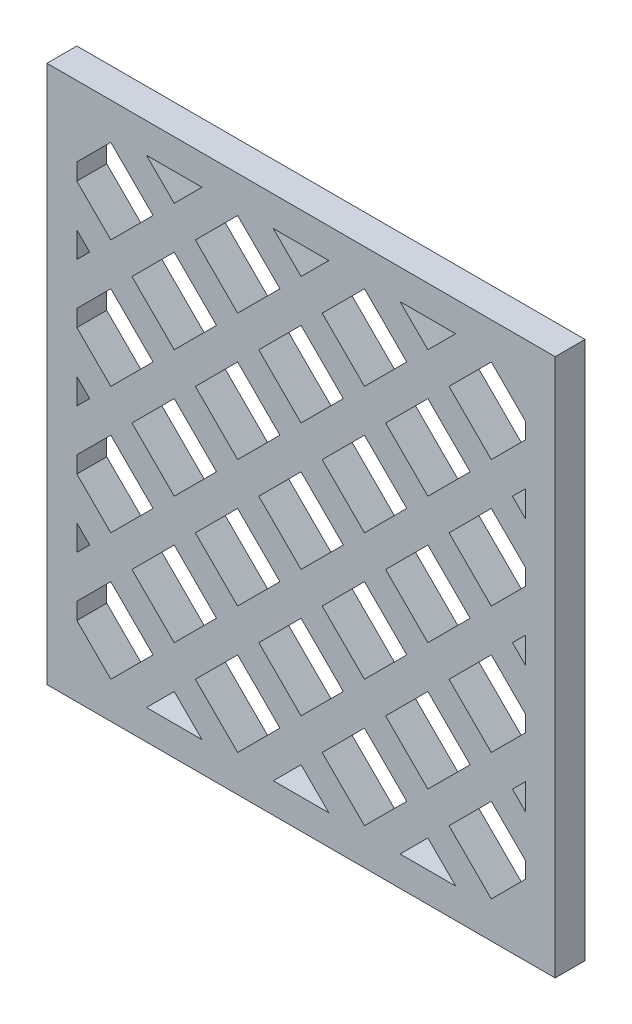
SolidWorks part; units mm, degrees
material "Balsa"
ref_plane "Alzado" through (0, 0, 0) normal (0, 0, 1) x (1, 0, 0)
ref_plane "Planta" through (0, 0, 0) normal (0, 1, 0) x (1, 0, 0)
ref_plane "Vista lateral" through (0, 0, 0) normal (1, 0, 0) x (0, 0, -1)
sketch "Croquis1" plane through (0, 0, 0) normal (0, 0, 1) x (1, 0, 0)
  line L0 (-75.1581, 75.2999) -> (-75.1581, -4.7001) construction
  line L1 (-80.1581, 80.2999) -> (4.8419, 80.2999)
  line L2 (-80.1581, 80.2999) -> (-80.1581, -9.7001)
  line L3 (-80.1581, -9.7001) -> (4.8419, -9.7001)
  line L4 (4.8419, 80.2999) -> (4.8419, -9.7001)
  line L5 (-75.1581, -4.7001) -> (-0.1581, -4.7001) construction
  line L6 (-0.1581, -4.7001) -> (-0.1581, 75.2999) construction
  line L7 (-0.1581, 75.2999) -> (-75.1581, 75.2999) construction
  line L8 (-37.6581, 80.2999) -> (-37.6581, -9.7001) construction
  line L9 (-80.1581, 35.2999) -> (4.8419, 35.2999) construction
  line L10 (-37.6581, 42.371) -> (-44.7291, 35.2999)
  line L11 (-44.7291, 35.2999) -> (-37.6581, 28.2288)
  line L12 (-37.6581, 28.2288) -> (-30.587, 35.2999)
  line L13 (-30.587, 35.2999) -> (-37.6581, 42.371)
  line L76 (-65.9423, 35.2999) -> (-58.8713, 28.2288)
  line L77 (-58.8713, 28.2288) -> (-51.8002, 35.2999)
  line L82 (-62.4068, 24.6933) -> (-69.4779, 31.7644)
  line L83 (-69.4779, 31.7644) -> (-75.1581, 26.0842)
  line L84 (-75.1581, 23.3024) -> (-69.4779, 17.6222)
  line L85 (-69.4779, 17.6222) -> (-62.4068, 24.6933)
  line L89 (-75.1581, 33.1552) -> (-72.8062, 35.5071)
  line L90 (-73.0134, 14.0867) -> (-75.1581, 16.2314)
  line L105 (-19.9804, 24.6933) -> (-27.0515, 31.7644)
  line L106 (-27.0515, 31.7644) -> (-34.1225, 24.6933)
  line L107 (-34.1225, 24.6933) -> (-27.0515, 17.6222)
  line L108 (-27.0515, 17.6222) -> (-19.9804, 24.6933)
  line L121 (-30.587, 14.0867) -> (-37.6581, 21.1578)
  line L122 (-37.6581, 21.1578) -> (-44.7291, 14.0867)
  line L123 (-44.7291, 14.0867) -> (-37.6581, 7.0156)
  line L124 (-37.6581, 7.0156) -> (-30.587, 14.0867)
  line L125 (-19.9804, 3.4801) -> (-27.0515, 10.5512)
  line L126 (-27.0515, 10.5512) -> (-34.1225, 3.4801)
  line L127 (-34.1225, 3.4801) -> (-27.0515, -3.591)
  line L128 (-27.0515, -3.591) -> (-19.9804, 3.4801)
  line L129 (-11.8002, -4.7001) -> (-16.4449, -0.0554)
  line L130 (-16.4449, -0.0554) -> (-21.0895, -4.7001)
  line L137 (-41.1936, 3.4801) -> (-48.2647, 10.5512)
  line L138 (-48.2647, 10.5512) -> (-55.3357, 3.4801)
  line L139 (-55.3357, 3.4801) -> (-48.2647, -3.591)
  line L140 (-48.2647, -3.591) -> (-41.1936, 3.4801)
  line L141 (-33.0134, -4.7001) -> (-37.6581, -0.0554)
  line L142 (-37.6581, -0.0554) -> (-42.3027, -4.7001)
  line L153 (-54.2266, -4.7001) -> (-58.8713, -0.0554)
  line L154 (-58.8713, -0.0554) -> (-63.5159, -4.7001)
  line L169 (-41.1936, 24.6933) -> (-48.2647, 31.7644)
  line L170 (-48.2647, 31.7644) -> (-55.3357, 24.6933)
  line L171 (-55.3357, 24.6933) -> (-48.2647, 17.6222)
  line L172 (-48.2647, 17.6222) -> (-41.1936, 24.6933)
  line L181 (-19.9804, -38.9463) -> (-27.0515, -31.8752) [skipped]
  line L182 (-27.0515, -31.8752) -> (-34.1225, -38.9463) [skipped]
  line L183 (-34.1225, -38.9463) -> (-27.0515, -46.0174) [skipped]
  line L184 (-27.0515, -46.0174) -> (-19.9804, -38.9463) [skipped]
  line L185 (-9.3738, -28.3397) -> (-16.4449, -21.2686) [skipped]
  line L186 (-16.4449, -21.2686) -> (-23.5159, -28.3397) [skipped]
  line L187 (-23.5159, -28.3397) -> (-16.4449, -35.4108) [skipped]
  line L188 (-16.4449, -35.4108) -> (-9.3738, -28.3397) [skipped]
  line L189 (-30.587, -28.3397) -> (-37.6581, -21.2686) [skipped]
  line L190 (-37.6581, -21.2686) -> (-44.7291, -28.3397) [skipped]
  line L191 (-44.7291, -28.3397) -> (-37.6581, -35.4108) [skipped]
  line L192 (-37.6581, -35.4108) -> (-30.587, -28.3397) [skipped]
  line L193 (-41.1936, -17.7331) -> (-48.2647, -10.662) [skipped]
  line L194 (-48.2647, -10.662) -> (-55.3357, -17.7331) [skipped]
  line L195 (-55.3357, -17.7331) -> (-48.2647, -24.8042) [skipped]
  line L196 (-48.2647, -24.8042) -> (-41.1936, -17.7331) [skipped]
  line L197 (-19.9804, -17.7331) -> (-27.0515, -10.662) [skipped]
  line L198 (-27.0515, -10.662) -> (-34.1225, -17.7331) [skipped]
  line L199 (-34.1225, -17.7331) -> (-27.0515, -24.8042) [skipped]
  line L200 (-27.0515, -24.8042) -> (-19.9804, -17.7331) [skipped]
  line L201 (1.2328, -17.7331) -> (-5.8383, -10.662) [skipped]
  line L202 (-5.8383, -10.662) -> (-12.9093, -17.7331) [skipped]
  line L203 (-12.9093, -17.7331) -> (-5.8383, -24.8042) [skipped]
  line L204 (-5.8383, -24.8042) -> (1.2328, -17.7331) [skipped]
  line L205 (11.8394, -7.1265) -> (4.7683, -0.0554) [skipped]
  line L206 (4.7683, -0.0554) -> (-2.3027, -7.1265) [skipped]
  line L207 (-2.3027, -7.1265) -> (4.7683, -14.1976) [skipped]
  line L208 (4.7683, -14.1976) -> (11.8394, -7.1265) [skipped]
  line L209 (-65.9423, -7.1265) -> (-58.8713, -14.1976) [skipped]
  line L210 (-58.8713, -14.1976) -> (-51.8002, -7.1265) [skipped]
  line L211 (-44.7291, -7.1265) -> (-37.6581, -14.1976) [skipped]
  line L212 (-37.6581, -14.1976) -> (-30.587, -7.1265) [skipped]
  line L213 (-23.5159, -7.1265) -> (-16.4449, -14.1976) [skipped]
  line L214 (-16.4449, -14.1976) -> (-9.3738, -7.1265) [skipped]
  line L216 (-63.5159, -4.7001) -> (-54.2266, -4.7001)
  line L217 (-42.3027, -4.7001) -> (-33.0134, -4.7001)
  line L218 (-21.0895, -4.7001) -> (-11.8002, -4.7001)
  line L221 (-75.1581, 11.942) -> (-73.0134, 14.0867)
  line L226 (-51.8002, 14.0867) -> (-58.8713, 21.1578)
  line L227 (-58.8713, 21.1578) -> (-65.9423, 14.0867)
  line L228 (-65.9423, 14.0867) -> (-58.8713, 7.0156)
  line L229 (-58.8713, 7.0156) -> (-51.8002, 14.0867)
  line L230 (-62.4068, 3.4801) -> (-69.4779, 10.5512)
  line L231 (-69.4779, 10.5512) -> (-75.1581, 4.871)
  line L232 (-75.1581, 2.0892) -> (-69.4779, -3.591)
  line L233 (-69.4779, -3.591) -> (-62.4068, 3.4801)
  line L234 (-75.1581, 37.4446) -> (-75.1581, 33.1552)
  line L235 (-75.1581, 4.871) -> (-75.1581, 2.0892)
  line L236 (-75.1581, 26.0842) -> (-75.1581, 23.3024)
  line L237 (-75.1581, 16.2314) -> (-75.1581, 11.942)
  line L240 (-23.5159, 35.2999) -> (-16.4449, 28.2288)
  line L241 (-16.4449, 28.2288) -> (-9.3738, 35.2999)
  line L246 (-0.1581, 26.0842) -> (-5.8383, 31.7644)
  line L247 (-5.8383, 31.7644) -> (-12.9093, 24.6933)
  line L248 (-12.9093, 24.6933) -> (-5.8383, 17.6222)
  line L249 (-5.8383, 17.6222) -> (-0.1581, 23.3024)
  line L252 (-2.3027, 35.2999) -> (-0.1581, 33.1552)
  line L255 (-0.1581, 16.2314) -> (-2.3027, 14.0867)
  line L256 (-2.3027, 14.0867) -> (-0.1581, 11.942)
  line L262 (-9.3738, 14.0867) -> (-16.4449, 21.1578)
  line L263 (-83.62, 24.6933) -> (-90.6911, 31.7644) [skipped]
  line L264 (-90.6911, 31.7644) -> (-97.7621, 24.6933) [skipped]
  line L265 (-97.7621, 24.6933) -> (-90.6911, 17.6222) [skipped]
  line L266 (-90.6911, 17.6222) -> (-83.62, 24.6933) [skipped]
  line L267 (-80.0845, 21.1578) -> (-87.1555, 14.0867) [skipped]
  line L268 (-87.1555, 14.0867) -> (-80.0845, 7.0156) [skipped]
  line L269 (-87.1555, 35.2999) -> (-80.0845, 28.2288) [skipped]
  line L270 (-80.0845, 42.371) -> (-87.1555, 35.2999) [skipped]
  line L271 (-51.8002, 35.2999) -> (-58.8713, 42.371) [skipped]
  line L272 (-58.8713, 42.371) -> (-65.9423, 35.2999) [skipped]
  line L273 (-69.4779, 38.8354) -> (-62.4068, 45.9065) [skipped]
  line L274 (-62.4068, 45.9065) -> (-69.4779, 52.9776) [skipped]
  line L275 (-74.9509, 47.5045) -> (-76.3418, 46.1137) [skipped]
  line L276 (-76.5489, 45.9065) -> (-75.1581, 44.5156) [skipped]
  line L277 (-75.1581, 2.0892) -> (-69.4779, -3.591) [skipped]
  line L278 (-69.4779, -3.591) -> (-62.4068, 3.4801) [skipped]
  line L279 (-62.4068, 3.4801) -> (-69.4779, 10.5512) [skipped]
  line L280 (-69.2707, 10.7583) -> (-74.9509, 5.0781) [skipped]
  line L281 (-51.8002, 14.0867) -> (-58.8713, 21.1578) [skipped]
  line L282 (-58.8713, 21.1578) -> (-65.9423, 14.0867) [skipped]
  line L283 (-65.9423, 14.0867) -> (-58.8713, 7.0156) [skipped]
  line L284 (-58.8713, 7.0156) -> (-51.8002, 14.0867) [skipped]
  line L285 (-73.0134, 35.2999) -> (-75.1581, 37.4446) [skipped]
  line L286 (-16.4449, 21.1578) -> (-23.5159, 14.0867)
  line L287 (-23.5159, 14.0867) -> (-16.4449, 7.0156)
  line L288 (-16.4449, 7.0156) -> (-9.3738, 14.0867)
  line L289 (-0.1581, 4.871) -> (-5.8383, 10.5512)
  line L290 (-5.8383, 10.5512) -> (-12.9093, 3.4801)
  line L291 (-12.9093, 3.4801) -> (-5.8383, -3.591)
  line L292 (-5.8383, -3.591) -> (-0.1581, 2.0892)
  line L293 (22.446, 24.6933) -> (15.3749, 31.7644) [skipped]
  line L294 (15.3749, 31.7644) -> (8.3039, 24.6933) [skipped]
  line L295 (8.3039, 24.6933) -> (15.3749, 17.6222) [skipped]
  line L296 (15.3749, 17.6222) -> (22.446, 24.6933) [skipped]
  line L297 (11.8394, 35.2999) -> (4.7683, 42.371) [skipped]
  line L298 (4.7683, 28.2288) -> (11.8394, 35.2999) [skipped]
  line L299 (11.8394, 14.0867) -> (4.7683, 21.1578) [skipped]
  line L300 (4.7683, 7.0156) -> (11.8394, 14.0867) [skipped]
  line L301 (1.2328, 45.9065) -> (-5.8383, 52.9776) [skipped]
  line L302 (-5.8383, 52.9776) -> (-12.9093, 45.9065) [skipped]
  line L303 (-12.9093, 45.9065) -> (-5.8383, 38.8354) [skipped]
  line L304 (-5.8383, 38.8354) -> (1.2328, 45.9065) [skipped]
  line L305 (-16.4449, 42.371) -> (-23.5159, 35.2999) [skipped]
  line L306 (-9.3738, 35.2999) -> (-16.4449, 42.371) [skipped]
  line L307 (0.0491, 37.6517) -> (-2.0955, 35.5071) [skipped]
  line L308 (-9.3738, 14.0867) -> (-16.4449, 21.1578) [skipped]
  line L309 (-16.4449, 21.1578) -> (-23.5159, 14.0867) [skipped]
  line L310 (-23.5159, 14.0867) -> (-16.4449, 7.0156) [skipped]
  line L311 (-16.4449, 7.0156) -> (-9.3738, 14.0867) [skipped]
  line L312 (-5.6311, -3.3838) -> (0.0491, 2.2964) [skipped]
  line L313 (-12.9093, 3.4801) -> (-5.8383, -3.591) [skipped]
  line L314 (-5.8383, 10.5512) -> (-12.9093, 3.4801) [skipped]
  line L315 (-0.1581, 4.871) -> (-5.8383, 10.5512) [skipped]
  line L316 (-0.1581, 4.871) -> (-0.1581, 2.0892)
  line L317 (-0.1581, 11.942) -> (-0.1581, 16.2314)
  line L318 (-0.1581, 23.3024) -> (-0.1581, 26.0842)
  line L319 (-0.1581, 33.1552) -> (-0.1581, 37.4446)
  line L320 (-2.3027, 35.2999) -> (-0.1581, 37.4446)
  line L321 (-16.4449, 42.371) -> (-9.3738, 35.2999)
  line L322 (-23.5159, 35.2999) -> (-16.4449, 42.371)
  line L323 (-58.8713, 42.371) -> (-51.8002, 35.2999)
  line L324 (-65.9423, 35.2999) -> (-58.8713, 42.371)
  line L325 (-75.1581, 37.4446) -> (-72.8062, 35.0927)
  line L326 (-48.2647, 52.9776) -> (-41.1936, 45.9065)
  line L327 (-55.3357, 45.9065) -> (-48.2647, 52.9776)
  line L328 (-48.2647, 38.8354) -> (-55.3357, 45.9065)
  line L329 (-41.1936, 45.9065) -> (-48.2647, 38.8354)
  line L330 (-27.0515, 52.9776) -> (-19.9804, 45.9065)
  line L331 (-34.1225, 45.9065) -> (-27.0515, 52.9776)
  line L332 (-27.0515, 38.8354) -> (-34.1225, 45.9065)
  line L333 (-19.9804, 45.9065) -> (-27.0515, 38.8354)
  line L334 (-37.6581, 63.5842) -> (-30.587, 56.5131)
  line L335 (-44.7291, 56.5131) -> (-37.6581, 63.5842)
  line L336 (-37.6581, 49.442) -> (-44.7291, 56.5131)
  line L337 (-30.587, 56.5131) -> (-37.6581, 49.442)
  line L338 (-2.3027, 56.5131) -> (-0.1581, 58.6578)
  line L339 (-0.1581, 54.3684) -> (-2.3027, 56.5131)
  line L340 (-0.1581, 58.6578) -> (-0.1581, 54.3684)
  line L341 (-5.8383, 52.9776) -> (-0.1581, 47.2974)
  line L342 (-12.9093, 45.9065) -> (-5.8383, 52.9776)
  line L343 (-5.8383, 38.8354) -> (-12.9093, 45.9065)
  line L344 (-0.1581, 44.5156) -> (-5.8383, 38.8354)
  line L345 (-0.1581, 47.2974) -> (-0.1581, 44.5156)
  line L346 (-16.4449, 63.5842) -> (-9.3738, 56.5131)
  line L347 (-23.5159, 56.5131) -> (-16.4449, 63.5842)
  line L348 (-16.4449, 49.442) -> (-23.5159, 56.5131)
  line L349 (-9.3738, 56.5131) -> (-16.4449, 49.442)
  line L350 (-0.1581, 65.7288) -> (-5.8383, 60.0486)
  line L351 (-5.8383, 60.0486) -> (-12.9093, 67.1197)
  line L352 (-12.9093, 67.1197) -> (-5.8383, 74.1908)
  line L353 (-5.8383, 74.1908) -> (-0.1581, 68.5106)
  line L354 (-0.1581, 65.7288) -> (-0.1581, 68.5106)
  line L355 (-16.4449, 70.6552) -> (-21.0895, 75.2999)
  line L356 (-11.8002, 75.2999) -> (-16.4449, 70.6552)
  line L357 (-21.0895, 75.2999) -> (-11.8002, 75.2999)
  line L358 (-27.0515, 74.1908) -> (-19.9804, 67.1197)
  line L359 (-34.1225, 67.1197) -> (-27.0515, 74.1908)
  line L360 (-27.0515, 60.0486) -> (-34.1225, 67.1197)
  line L361 (-19.9804, 67.1197) -> (-27.0515, 60.0486)
  line L362 (-37.6581, 70.6552) -> (-42.3027, 75.2999)
  line L363 (-33.0134, 75.2999) -> (-37.6581, 70.6552)
  line L364 (-42.3027, 75.2999) -> (-33.0134, 75.2999)
  line L365 (-58.8713, 70.6552) -> (-63.5159, 75.2999)
  line L366 (-54.2266, 75.2999) -> (-58.8713, 70.6552)
  line L367 (-63.5159, 75.2999) -> (-54.2266, 75.2999)
  line L368 (-48.2647, 74.1908) -> (-41.1936, 67.1197)
  line L369 (-55.3357, 67.1197) -> (-48.2647, 74.1908)
  line L370 (-48.2647, 60.0486) -> (-55.3357, 67.1197)
  line L371 (-41.1936, 67.1197) -> (-48.2647, 60.0486)
  line L372 (-58.8713, 63.5842) -> (-51.8002, 56.5131)
  line L373 (-65.9423, 56.5131) -> (-58.8713, 63.5842)
  line L374 (-58.8713, 49.442) -> (-65.9423, 56.5131)
  line L375 (-51.8002, 56.5131) -> (-58.8713, 49.442)
  line L376 (-69.4779, 60.0486) -> (-75.1581, 65.7288)
  line L377 (-62.4068, 67.1197) -> (-69.4779, 60.0486)
  line L378 (-69.4779, 74.1908) -> (-62.4068, 67.1197)
  line L379 (-75.1581, 68.5106) -> (-69.4779, 74.1908)
  line L380 (-75.1581, 65.7288) -> (-75.1581, 68.5106)
  line L381 (-73.0134, 56.5131) -> (-75.1581, 54.3684)
  line L382 (-75.1581, 58.6578) -> (-73.0134, 56.5131)
  line L383 (-75.1581, 54.3684) -> (-75.1581, 58.6578)
  line L384 (-69.4779, 38.8354) -> (-75.1581, 44.5156)
  line L385 (-62.4068, 45.9065) -> (-69.4779, 38.8354)
  line L386 (-69.4779, 52.9776) -> (-62.4068, 45.9065)
  line L387 (-75.1581, 47.2974) -> (-69.4779, 52.9776)
  line L388 (-75.1581, 44.5156) -> (-75.1581, 47.2974)
  point P41 (-75.1581, 35.2999)
  point P60 (-0.1581, 35.2999)
  point P64 (-75.1581, 35.2999)
  dimension "D1" = 90
  dimension "D2" = 85
  dimension "D3" = 75
  dimension "D5" = 5
  dimension "D6" = 5
  dimension "D7" = 3
  dimension "D10" = 10
  dimension "D11" = 5
  dimension "D12" = 4
  dimension "D8" = 3
  dimension "D9" = 3
  dimension "D13" = 3
extrude "Saliente-Extruir1" add sketch "Croquis1" along normal blind 5 contours L4 L1 L2 L3 L354 L350 L351 L352 L353 L318 L249 L248 L247 L246 L317 L256 L255 L288 L287 L286 L262 L237 L90 L221 L236 L83 L82 L85 L84 L235 L231 L230 L233 L232 L229 L228 L227 L226 L218 L130 L129
